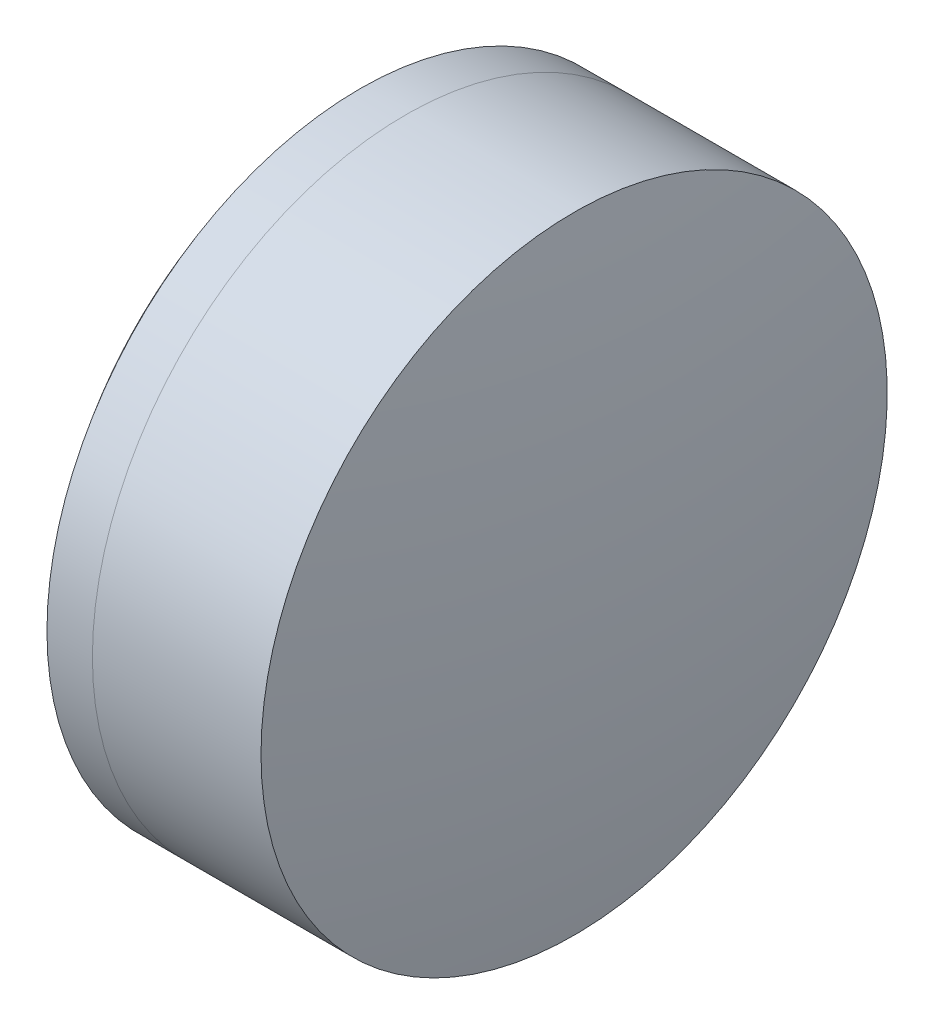
SolidWorks part; units mm, degrees
ref_plane "前视基准面" through (0, 0, 0) normal (0, 0, 1) x (1, 0, 0)
ref_plane "上视基准面" through (0, 0, 0) normal (0, 1, 0) x (1, 0, 0)
ref_plane "右视基准面" through (0, 0, 0) normal (1, 0, 0) x (0, 0, -1)
sketch "草图1" plane through (0, 0, 0) normal (0, 1, 0) x (1, 0, 0)
  line L0 (-9.7026, 0) -> (242.9656, 0) construction
  line L1 (219.5409, -12.7) -> (221.384, -12.7)
  line L2 (219.5409, 12.7) -> (221.384, 12.7)
  arc A0 (221.384, -12.7) -> (221.384, 12.7) centre (210.5397, 0) ccw
  arc A1 (219.5409, 12.7) -> (219.5409, -12.7) centre (236.1397, 0) ccw
  point P10 (215.2397, 0)
  point P11 (227.2397, 0)
  dimension "D3" = 20.9
  dimension "D4" = 16.7
  dimension "D1" = 12.7
  dimension "D2" = 12.7
  dimension "D5" = 12
revolve "旋转1" add sketch "草图1" angle 360 about L0
sketch "草图2" plane through (0, 0, 0) normal (0, 1, 0) x (1, 0, 0)
  line L0 (-0.5519, 0) -> (253.9868, 0) construction
  line L2 (221.384, 12.7) -> (228.2226, 12.7)
  line L3 (221.384, -12.7) -> (228.2226, -12.7)
  arc A0 (228.2226, -12.7) -> (228.2226, 12.7) centre (149.4397, 0) ccw
  arc A1 (221.384, -12.7) -> (221.384, 12.7) centre (210.5397, 0) ccw construction
  arc A2 (221.384, -12.7) -> (221.384, 12.7) centre (210.5397, 0) ccw
  point P4 (227.2397, 0)
  point P8 (229.2397, 0)
  dimension "D1" = 79.8
  dimension "D2" = 2
revolve "旋转3" add sketch "草图2" angle 360 about L0
